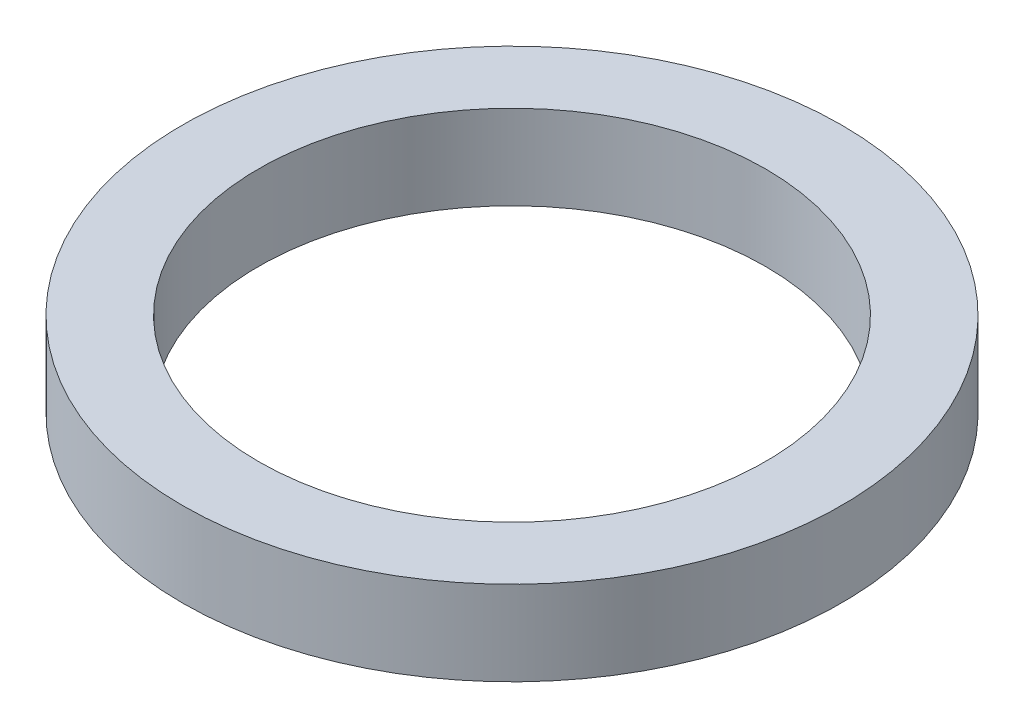
SolidWorks part; units mm, degrees
material "1060 Alloy"
ref_plane "Front Plane" through (0, 0, 0) normal (0, 0, 1) x (1, 0, 0)
ref_plane "Top Plane" through (0, 0, 0) normal (0, 1, 0) x (1, 0, 0)
ref_plane "Right Plane" through (0, 0, 0) normal (1, 0, 0) x (0, 0, -1)
sketch "Sketch1" plane through (0, 0, 0) normal (0, 1, 0) x (1, 0, 0)
  circle A0 centre (0, 0) radius 39
  circle A1 centre (0, 0) radius 30
  dimension "D1" = 78
  dimension "D2" = 60
extrude "Boss-Extrude1" add sketch "Sketch1" along normal blind 10
